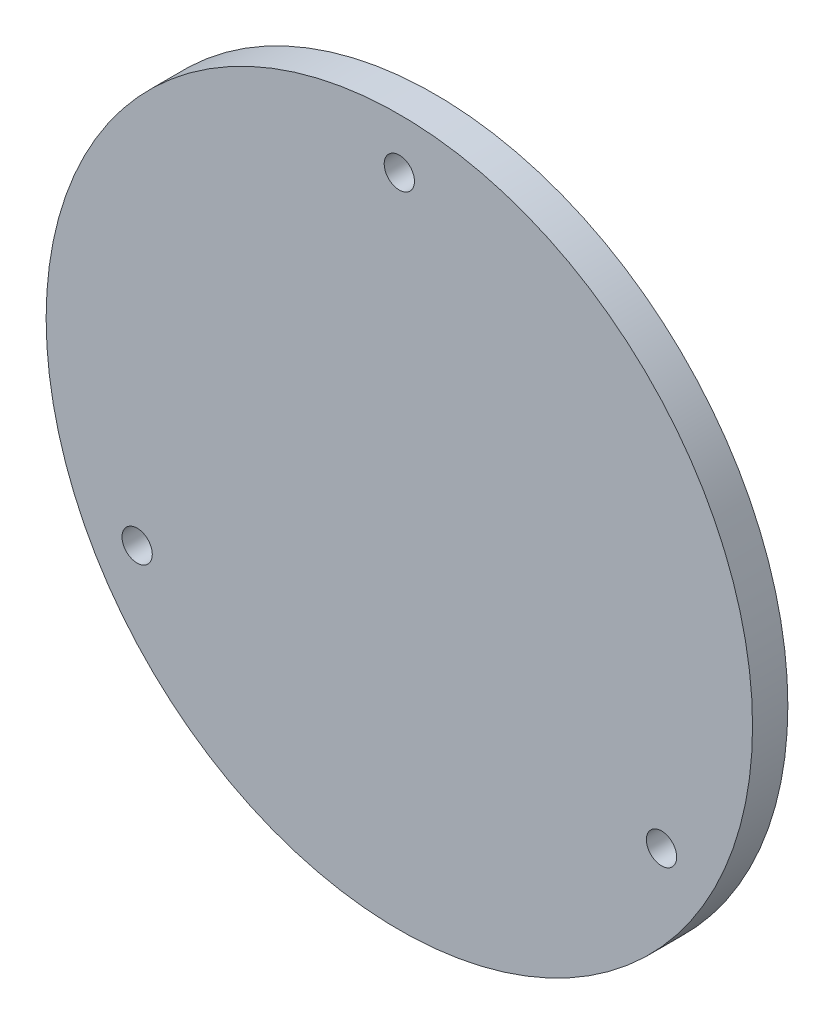
SolidWorks part; units mm, degrees
ref_plane "Front Plane" through (0, 0, 0) normal (0, 0, 1) x (1, 0, 0)
ref_plane "Top Plane" through (0, 0, 0) normal (0, 1, 0) x (1, 0, 0)
ref_plane "Right Plane" through (0, 0, 0) normal (1, 0, 0) x (0, 0, -1)
sketch "Sketch1" plane through (0, 0, 0) normal (0, 0, 1) x (1, 0, 0)
  circle A0 centre (0, 0) radius 70
extrude "Boss-Extrude1" add sketch "Sketch1" along normal blind 7
sketch "Sketch2" plane through (0, 0, 0) normal (0, 0, -1) x (-1, 0, 0)
  circle A0 centre (0, 0) radius 55
  circle A1 centre (0, 0) radius 50
extrude "Boss-Extrude2" add sketch "Sketch2" along normal blind 3
sketch "Sketch3" plane through (0, 0, 7) normal (0, 0, 1) x (1, 0, 0)
  circle A0 centre (0, 0) radius 60
  circle A1 centre (0, 60) radius 3
  circle A2 centre (51.9615, -30) radius 3
  circle A3 centre (-51.9615, -30) radius 3
  point P11 (0, 0)
  dimension "D1" = 3
extrude "Cut-Extrude1" cut sketch "Sketch3" against normal through all contours A0 A3 | A2 | A1
